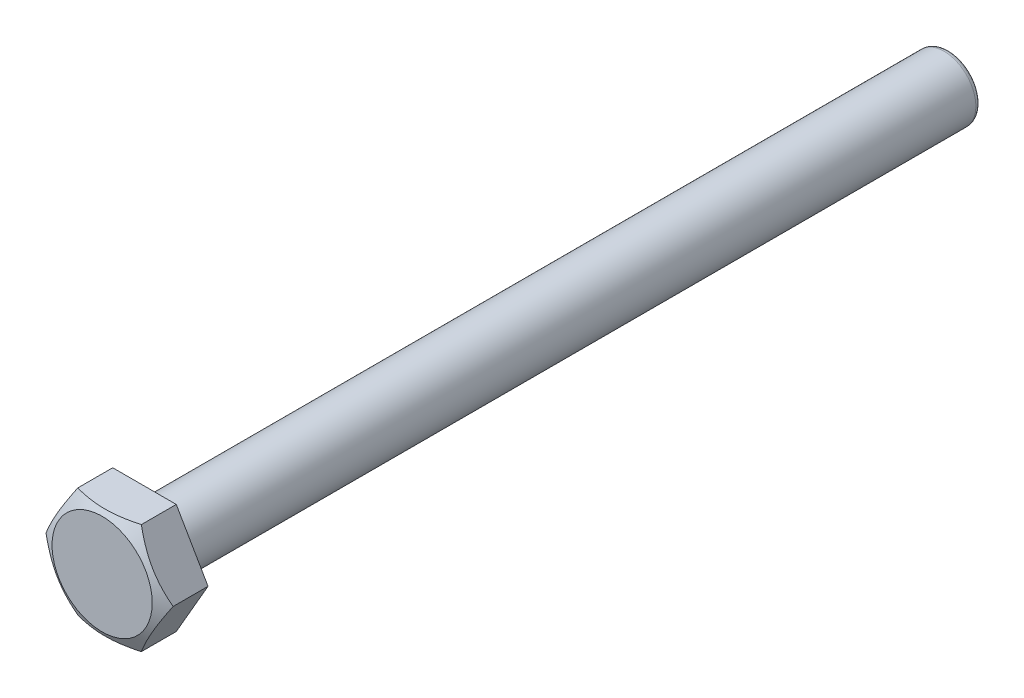
SolidWorks part; units mm, degrees
material "1023 Carbon Steel Sheet (SS)"
ref_plane "Front Plane" through (0, 0, 0) normal (0, 0, 1) x (1, 0, 0)
ref_plane "Top Plane" through (0, 0, 0) normal (0, 1, 0) x (1, 0, 0)
ref_plane "Right Plane" through (0, 0, 0) normal (1, 0, 0) x (0, 0, -1)
sketch "Sketch1" plane through (0, 0, 0) normal (0, 0, 1) x (1, 0, 0)
  line L1 (6, 0) -> (3, 5.1962)
  line L2 (3, 5.1962) -> (-3, 5.1962)
  line L3 (-3, 5.1962) -> (-6, 0)
  line L4 (-6, 0) -> (-3, -5.1962)
  line L5 (-3, -5.1962) -> (3, -5.1962)
  line L6 (3, -5.1962) -> (6, 0)
  circle A0 centre (0, 0) radius 5.1962 construction
  dimension "D1" = 6
extrude "Boss-Extrude1" add sketch "Sketch1" along normal blind 4
sketch "Sketch2" plane through (0, 0, 4) normal (0, 0, 1) x (1, 0, 0)
  circle A0 centre (0, 0) radius 4.7297
ref_plane "Plane2" through (0, 0, 0) normal (0.866, 0.5, 0) x (0, 0, -1)
sketch "Sketch4" plane through (0, 0, 0) normal (0.866, 0.5, 0) x (0, 0, -1)
  line L0 (-4, 4.7297) -> (-3.3, 6)
  line L1 (-4, 4.7297) -> (-4, -4.7297) construction
  line L2 (-4, 3) -> (-4, 6) construction
  line L3 (-4, 6) -> (0, 6) construction
  line L4 (-3.3, 6) -> (-4, 6)
  line L5 (-4, 6) -> (-4, 4.7297)
  line L6 (-6.2252, 0) -> (3.1253, 0) construction
  dimension "D1" = 0.7
revolve "Cut-Revolve1" cut sketch "Sketch4" angle 360 about L6
sketch "Sketch5" plane through (0, 0, 0) normal (0, 0, -1) x (-1, 0, 0)
  circle A0 centre (0, 0) radius 3
  dimension "D1" = 6
extrude "Boss-Extrude2" add sketch "Sketch5" along normal blind 76
fillet "Fillet1" radius 0.5 1 edges at (-3, 0, -76)
